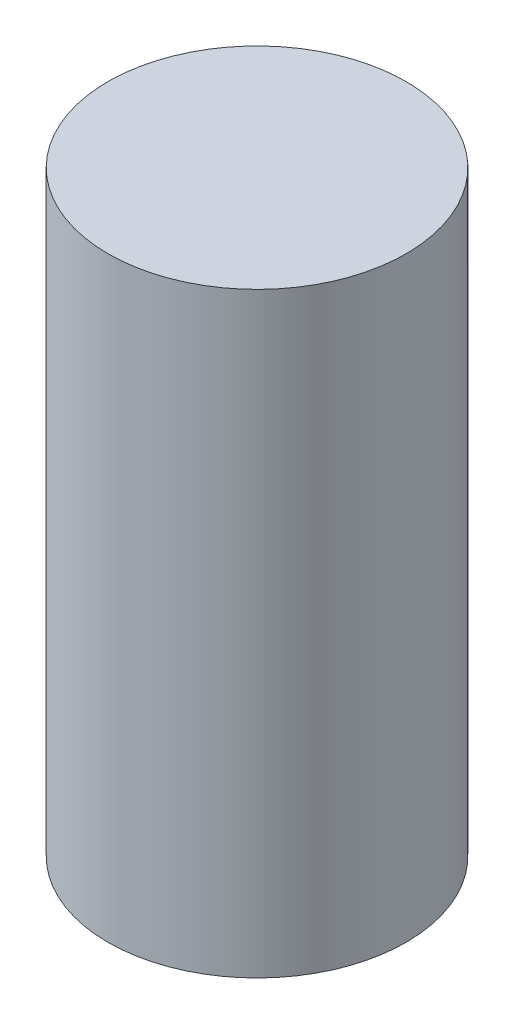
SolidWorks part; units mm, degrees
ref_plane "Ebene vorne" through (0, 0, 0) normal (0, 0, 1) x (1, 0, 0)
ref_plane "Ebene oben" through (0, 0, 0) normal (0, 1, 0) x (1, 0, 0)
ref_plane "Ebene rechts" through (0, 0, 0) normal (1, 0, 0) x (0, 0, -1)
sketch "Skizze1" plane through (0, 0, 0) normal (0, 1, 0) x (1, 0, 0)
  circle A0 centre (0, 0) radius 12.5
extrude "Aufsatz-Linear austragen1" add sketch "Skizze1" along normal blind 50
